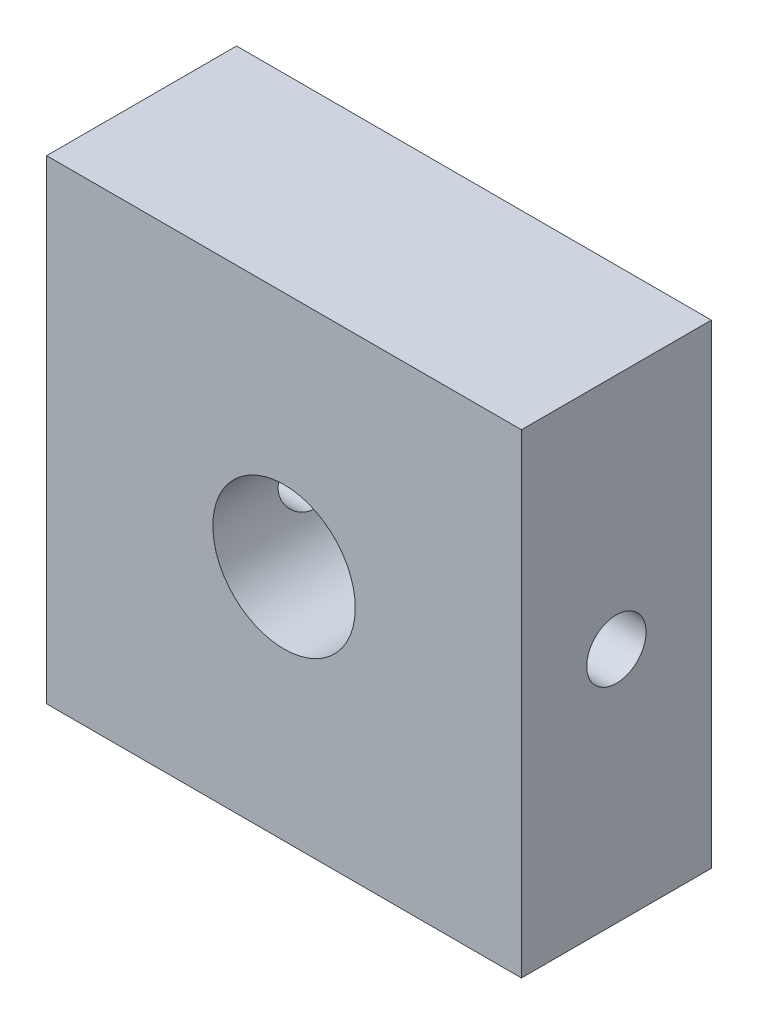
SolidWorks part; units mm, degrees
ref_plane "Front Plane" through (0, 0, 0) normal (0, 0, 1) x (1, 0, 0)
ref_plane "Top Plane" through (0, 0, 0) normal (0, 1, 0) x (1, 0, 0)
ref_plane "Right Plane" through (0, 0, 0) normal (1, 0, 0) x (0, 0, -1)
sketch "Sketch1" plane through (0, 0, 0) normal (0, 0, 1) x (1, 0, 0)
  line L1 (-172.6465, -146.3663) -> (-152.6465, -146.3663)
  line L2 (-172.6465, -146.3663) -> (-172.6465, -126.3663)
  line L3 (-172.6465, -126.3663) -> (-152.6465, -126.3663)
  line L4 (-152.6465, -146.3663) -> (-152.6465, -126.3663)
  line L5 (-172.6465, -146.3663) -> (-152.6465, -126.3663) construction
  line L6 (-172.6465, -126.3663) -> (-152.6465, -146.3663) construction
  point P0 (-162.6465, -136.3663)
  point P5 (0, 0)
  point P6 (-162.6465, -136.3663)
extrude "Boss-Extrude1" add sketch "Sketch1" along normal blind 8
sketch "Sketch2" plane through (0, 0, 8) normal (0, 0, 1) x (1, 0, 0)
  circle A0 centre (-162.6465, -136.3663) radius 3
extrude "Cut-Extrude1" cut sketch "Sketch2" against normal through all
sketch "Sketch3" plane through (-152.6465, 0, 0) normal (1, 0, 0) x (0, 0, -1)
  line L0 (-4, -146.3663) -> (-4, -126.3663) construction
  line L1 (-8, -146.3663) -> (0, -146.3663) construction
  line L2 (-8, -126.3663) -> (0, -126.3663) construction
  circle A0 centre (-4, -136.3663) radius 1.25
extrude "Cut-Extrude2" cut sketch "Sketch3" against normal through all
